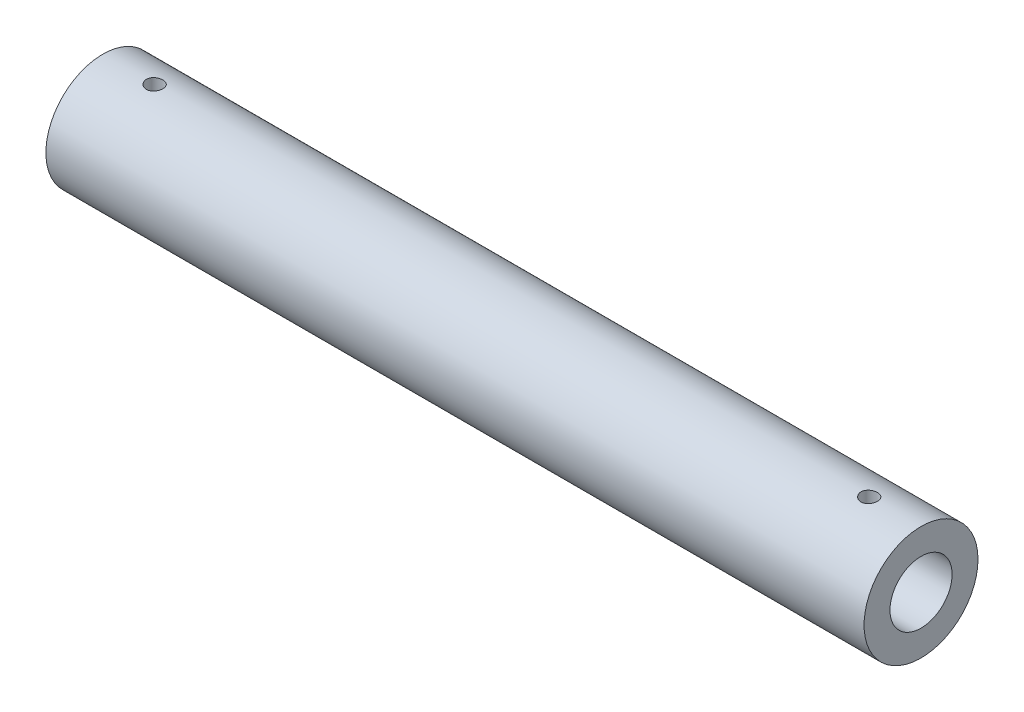
SolidWorks part; units mm, degrees
material "PVC Rigid"
ref_plane "Front Plane" through (0, 0, 0) normal (0, 0, 1) x (1, 0, 0)
ref_plane "Top Plane" through (0, 0, 0) normal (0, 1, 0) x (1, 0, 0)
ref_plane "Right Plane" through (0, 0, 0) normal (1, 0, 0) x (0, 0, -1)
sketch "Sketch2" plane through (0, 0, 0) normal (1, 0, 0) x (0, 0, -1)
  circle A0 centre (0, 0) radius 6
  circle A1 centre (0, 0) radius 11
  dimension "D1" = 5
  dimension "D2" = 12
extrude "Boss-Extrude1" add sketch "Sketch2" along normal blind 157.975
sketch "Sketch3" plane through (0, 0, 0) normal (0, 1, 0) x (1, 0, 0)
  line L0 (0, 0) -> (157.975, 0) construction
  line L1 (157.975, -11) -> (157.975, 11) construction
  circle A0 centre (10, 0) radius 1.5875
  circle A1 centre (147.975, 0) radius 1.5875
  dimension "D1" = 3.175
  dimension "D2" = 10
  dimension "D3" = 10
extrude "Cut-Extrude1" cut sketch "Sketch3" against normal through all and the other way through all
